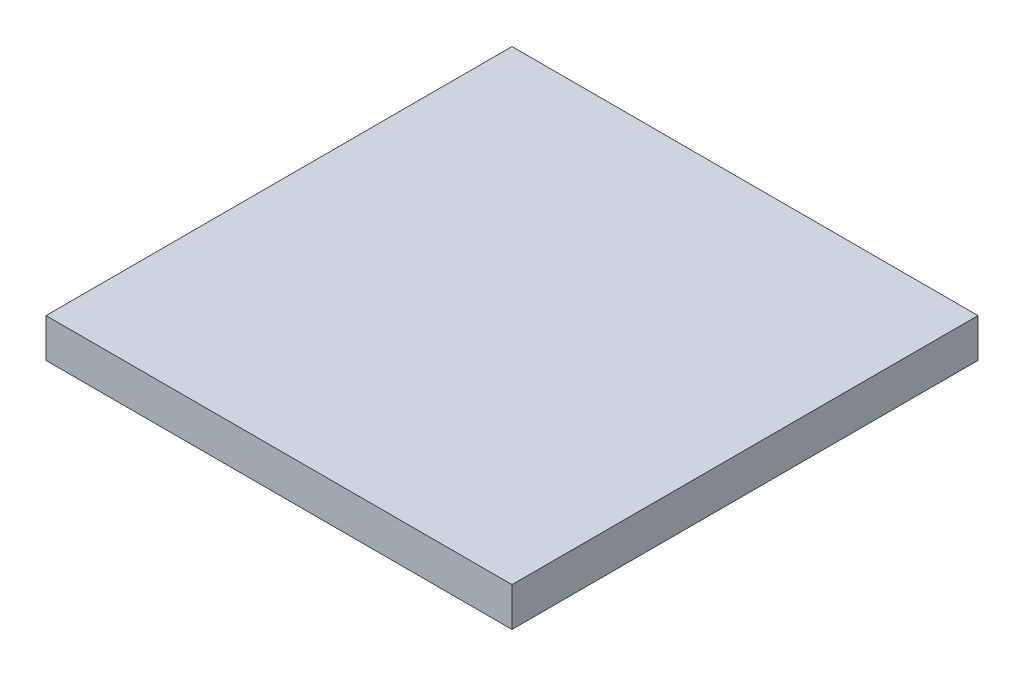
SolidWorks part; units mm, degrees
ref_plane "Front Plane" through (0, 0, 0) normal (0, 0, 1) x (1, 0, 0)
ref_plane "Top Plane" through (0, 0, 0) normal (0, 1, 0) x (1, 0, 0)
ref_plane "Right Plane" through (0, 0, 0) normal (1, 0, 0) x (0, 0, -1)
sketch "Sketch2" plane through (0, 0, 0) normal (0, 1, 0) x (1, 0, 0)
  line L1 (0, 0) -> (2400, 0)
  line L2 (0, 0) -> (0, 2400)
  line L3 (0, 2400) -> (2400, 2400)
  line L4 (2400, 0) -> (2400, 2400)
  dimension "D1" = 2400
  dimension "D2" = 2400
extrude "Boss-Extrude1" add sketch "Sketch2" along normal blind 200
